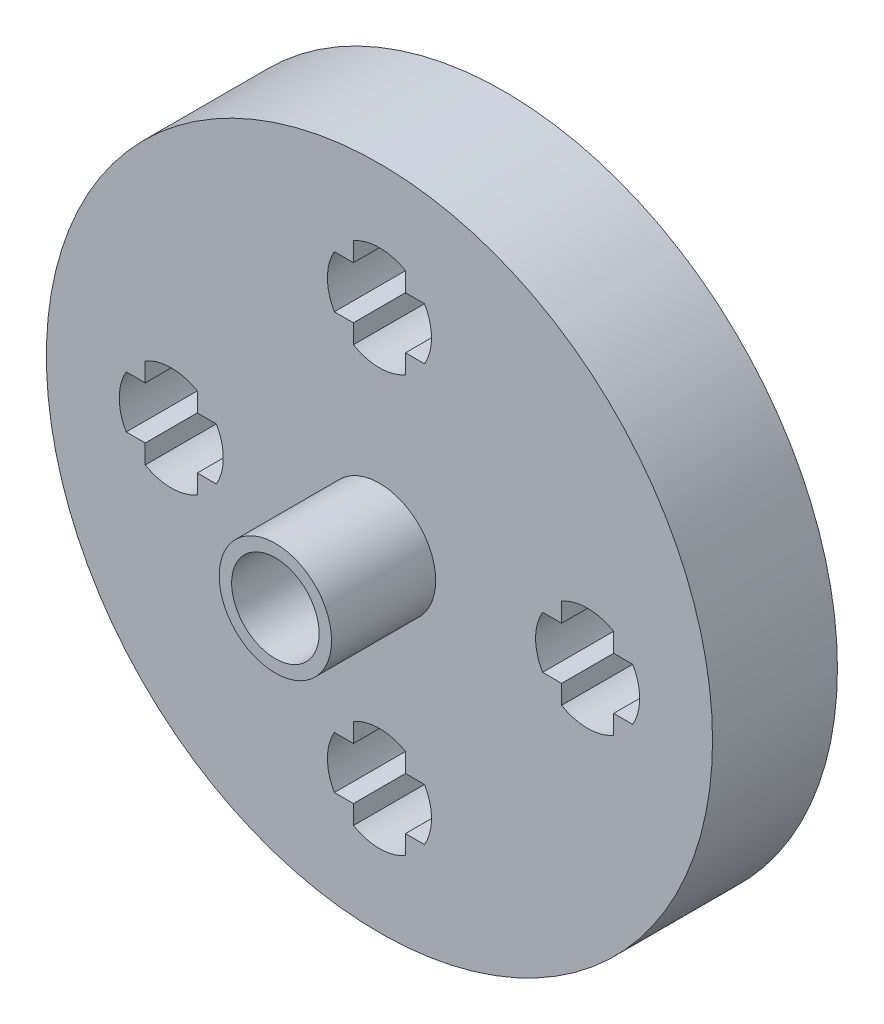
SolidWorks part; units mm, degrees
material "PLA"
ref_plane "Alzado" through (0, 0, 0) normal (0, 0, 1) x (1, 0, 0)
ref_plane "Planta" through (0, 0, 0) normal (0, 1, 0) x (1, 0, 0)
ref_plane "Vista lateral" through (0, 0, 0) normal (1, 0, 0) x (0, 0, -1)
sketch "Croquis1" plane through (0, 0, 0) normal (0, 0, 1) x (1, 0, 0)
  line L0 (0, 12.5) -> (0, 10) construction
  line L1 (0, 10) -> (2.5, 10) construction
  line L2 (0, 11.25) -> (2.1651, 11.25) construction
  line L3 (1.25, 10) -> (1.25, 12.1651) construction
  line L4 (2.1651, 11.25) -> (1.25, 11.25)
  line L5 (1.25, 11.25) -> (1.25, 12.1651)
  line L6 (1.25, 8.75) -> (2.1651, 8.75)
  line L7 (1.25, 7.8349) -> (1.25, 8.75)
  line L8 (-1.25, 8.75) -> (-1.25, 7.8349)
  line L9 (-2.1651, 8.75) -> (-1.25, 8.75)
  line L10 (-1.25, 11.25) -> (-2.1651, 11.25)
  line L11 (-1.25, 12.1651) -> (-1.25, 11.25)
  line L12 (11.25, -1.25) -> (12.1651, -1.25)
  line L13 (11.25, -2.1651) -> (11.25, -1.25)
  line L14 (8.75, -1.25) -> (8.75, -2.1651)
  line L15 (7.8349, -1.25) -> (8.75, -1.25)
  line L16 (8.75, 1.25) -> (7.8349, 1.25)
  line L17 (8.75, 2.1651) -> (8.75, 1.25)
  line L18 (11.25, 1.25) -> (11.25, 2.1651)
  line L19 (12.1651, 1.25) -> (11.25, 1.25)
  line L20 (-1.25, -11.25) -> (-1.25, -12.1651)
  line L21 (-2.1651, -11.25) -> (-1.25, -11.25)
  line L22 (-1.25, -8.75) -> (-2.1651, -8.75)
  line L23 (-1.25, -7.8349) -> (-1.25, -8.75)
  line L24 (1.25, -8.75) -> (1.25, -7.8349)
  line L25 (2.1651, -8.75) -> (1.25, -8.75)
  line L26 (1.25, -11.25) -> (2.1651, -11.25)
  line L27 (1.25, -12.1651) -> (1.25, -11.25)
  line L28 (-11.25, 1.25) -> (-12.1651, 1.25)
  line L29 (-11.25, 2.1651) -> (-11.25, 1.25)
  line L30 (-8.75, 1.25) -> (-8.75, 2.1651)
  line L31 (-7.8349, 1.25) -> (-8.75, 1.25)
  line L32 (-8.75, -1.25) -> (-7.8349, -1.25)
  line L33 (-8.75, -2.1651) -> (-8.75, -1.25)
  line L34 (-11.25, -1.25) -> (-11.25, -2.1651)
  line L35 (-12.1651, -1.25) -> (-11.25, -1.25)
  circle A0 centre (0, 0) radius 16
  circle A1 centre (0, 0) radius 10 construction
  circle A2 centre (0, 10) radius 2.5 construction
  arc A3 (0, 12.5) -> (1.25, 12.1651) centre (0, 10) cw
  arc A4 (2.1651, 11.25) -> (2.5, 10) centre (0, 10) cw
  arc A5 (2.5, 10) -> (2.1651, 8.75) centre (0, 10) cw
  arc A6 (1.25, 7.8349) -> (0, 7.5) centre (0, 10) cw
  arc A7 (0, 7.5) -> (-1.25, 7.8349) centre (0, 10) cw
  arc A8 (-2.1651, 8.75) -> (-2.5, 10) centre (0, 10) cw
  arc A9 (-2.5, 10) -> (-2.1651, 11.25) centre (0, 10) cw
  arc A10 (-1.25, 12.1651) -> (0, 12.5) centre (0, 10) cw
  arc A11 (12.1651, 1.25) -> (12.5, 0) centre (10, 0) cw
  arc A12 (12.5, 0) -> (12.1651, -1.25) centre (10, 0) cw
  arc A13 (11.25, -2.1651) -> (10, -2.5) centre (10, 0) cw
  arc A14 (10, -2.5) -> (8.75, -2.1651) centre (10, 0) cw
  arc A15 (7.8349, -1.25) -> (7.5, 0) centre (10, 0) cw
  arc A16 (7.5, 0) -> (7.8349, 1.25) centre (10, 0) cw
  arc A17 (8.75, 2.1651) -> (10, 2.5) centre (10, 0) cw
  arc A18 (10, 2.5) -> (11.25, 2.1651) centre (10, 0) cw
  arc A19 (1.25, -12.1651) -> (0, -12.5) centre (0, -10) cw
  arc A20 (0, -12.5) -> (-1.25, -12.1651) centre (0, -10) cw
  arc A21 (-2.1651, -11.25) -> (-2.5, -10) centre (0, -10) cw
  arc A22 (-2.5, -10) -> (-2.1651, -8.75) centre (0, -10) cw
  arc A23 (-1.25, -7.8349) -> (0, -7.5) centre (0, -10) cw
  arc A24 (0, -7.5) -> (1.25, -7.8349) centre (0, -10) cw
  arc A25 (2.1651, -8.75) -> (2.5, -10) centre (0, -10) cw
  arc A26 (2.5, -10) -> (2.1651, -11.25) centre (0, -10) cw
  arc A27 (-12.1651, -1.25) -> (-12.5, 0) centre (-10, 0) cw
  arc A28 (-12.5, 0) -> (-12.1651, 1.25) centre (-10, 0) cw
  arc A29 (-11.25, 2.1651) -> (-10, 2.5) centre (-10, 0) cw
  arc A30 (-10, 2.5) -> (-8.75, 2.1651) centre (-10, 0) cw
  arc A31 (-7.8349, 1.25) -> (-7.5, 0) centre (-10, 0) cw
  arc A32 (-7.5, 0) -> (-7.8349, -1.25) centre (-10, 0) cw
  arc A33 (-8.75, -2.1651) -> (-10, -2.5) centre (-10, 0) cw
  arc A34 (-10, -2.5) -> (-11.25, -2.1651) centre (-10, 0) cw
  point P33 (0, 10)
  point P92 (0, 0)
  dimension "D1" = 4
  dimension "D2" = 4
extrude "Saliente-Extruir1" add sketch "Croquis1" along normal blind 6 contours A0 L11 A10 A3 L5 L4 A4 A5 L6 L7 A6 A7 L8 L9 A8 A9 L10 A17 A18 L18 L19 A11 A12 L12 L13 A13 A14 L14 L15 A15 A16 L16 L17 A25 A26 L26 L27 A19 A20 L20 L21 A21 A22 L22 L23 A23 A24 L24
sketch "Croquis2" plane through (0, 0, 6) normal (0, 0, 1) x (1, 0, 0)
  circle A0 centre (0, 0) radius 2.7
  circle A1 centre (0, 0) radius 2.1
extrude "Saliente-Extruir2" add sketch "Croquis2" along normal blind 5
